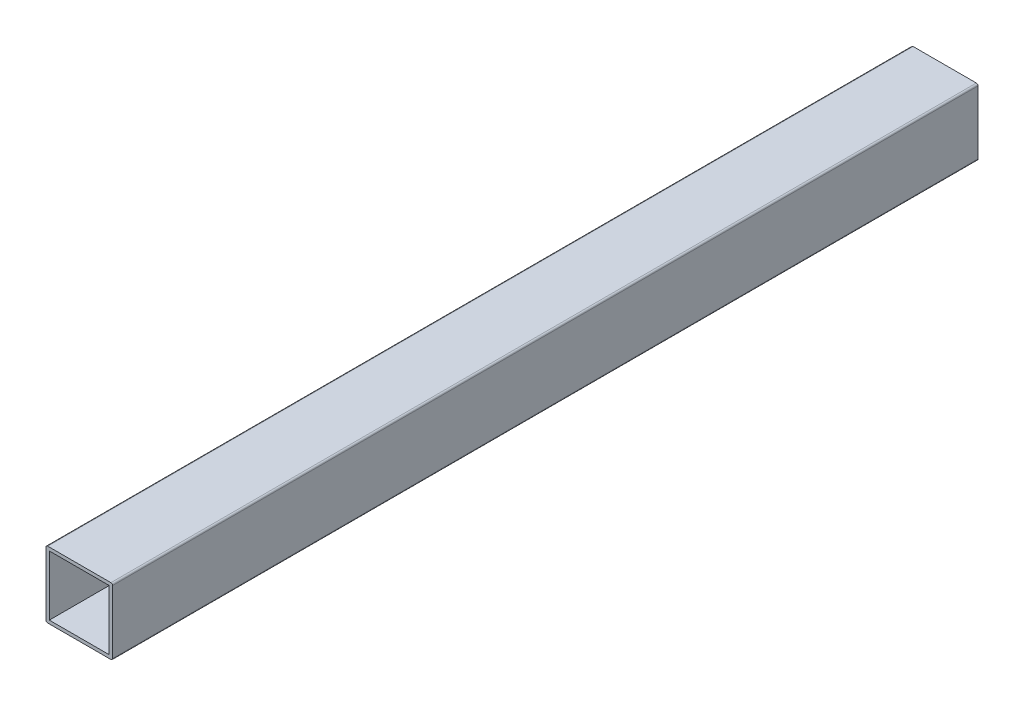
SolidWorks part; units mm, degrees
material "St.37"
ref_plane "Front Plane" through (0, 0, 0) normal (0, 0, 1) x (1, 0, 0)
ref_plane "Top Plane" through (0, 0, 0) normal (0, 1, 0) x (1, 0, 0)
ref_plane "Right Plane" through (0, 0, 0) normal (1, 0, 0) x (0, 0, -1)
sketch "Sketch1" plane through (0, 0, 0) normal (0, 0, 1) x (1, 0, 0)
  line L1 (-9.5, -10) -> (9.5, -10)
  line L2 (-10, -9.5) -> (-10, 9.5)
  line L3 (-9.5, 10) -> (9.5, 10)
  line L4 (10, -9.5) -> (10, 9.5)
  line L5 (-10, -10) -> (10, 10) construction
  line L6 (-10, 10) -> (10, -10) construction
  arc A0 (-9.5, -10) -> (-10, -9.5) centre (-9.5, -9.5) cw
  arc A1 (9.5, -10) -> (10, -9.5) centre (9.5, -9.5) ccw
  arc A2 (9.5, 10) -> (10, 9.5) centre (9.5, 9.5) cw
  arc A3 (-10, 9.5) -> (-9.5, 10) centre (-9.5, 9.5) cw
  point P0 (0, 0)
  dimension "D3" = 0.5
  dimension "D1" = 20
  dimension "D2" = 20
extrude "Extrude-Thin1" add sketch "Sketch1" along normal blind 260 thin
sketch "Sketch2" plane through (-10, 0, 0) normal (-1, 0, 0) x (0, 0, 1)
  line L0 (0, 9.5) -> (0, -9.5) construction
  line L1 (260, 9.5) -> (260, -9.5) construction
  line L2 (260, 10) -> (0, 10) construction
  line L3 (260, 9.5) -> (0, 9.5) construction
  circle A2 centre (64, 0) radius 3.4
  circle A3 centre (164, 0) radius 3.4
  circle A4 centre (196, 0) radius 3.4
  circle A5 centre (96, 0) radius 3.4
  dimension "D3" = 32
  dimension "D6" = 6.8
  dimension "D9" = 6.8
  dimension "D10" = 96
  dimension "D7" = 64
  dimension "D8" = 9.5
  dimension "D11" = 10
  dimension "D2" = 2
extrude "Cut-Extrude1" cut sketch "Sketch2" against normal blind 10
